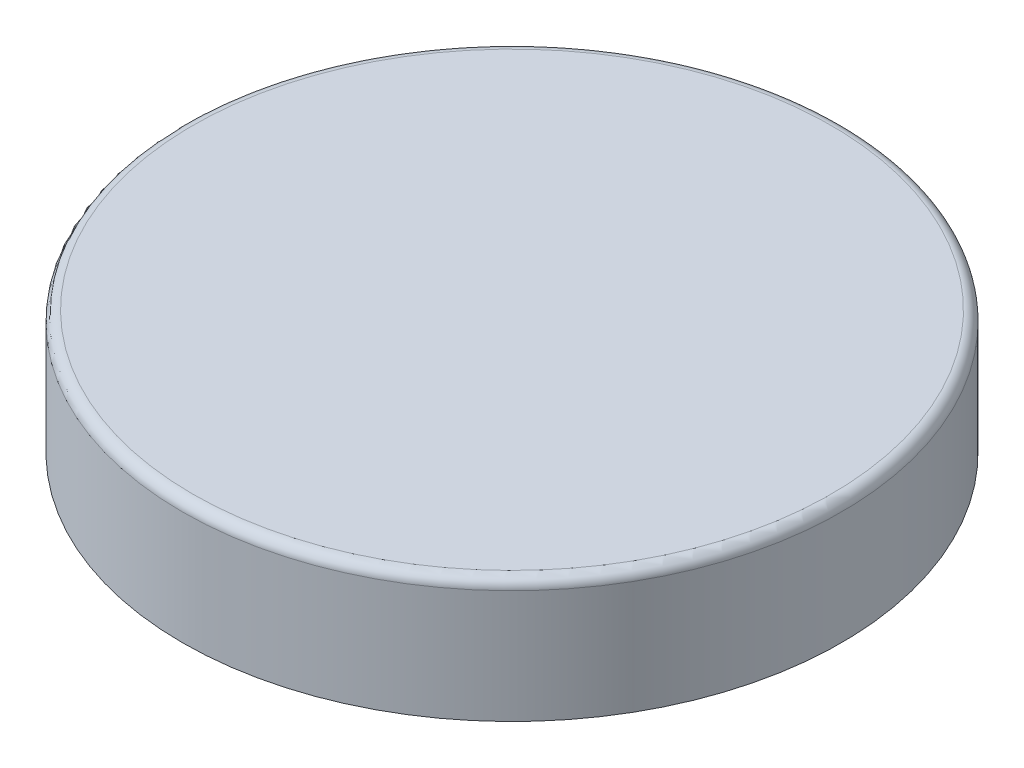
SolidWorks part; units mm, degrees
material "PLA Black"
ref_plane "Front Plane" through (0, 0, 0) normal (0, 0, 1) x (1, 0, 0)
ref_plane "Top Plane" through (0, 0, 0) normal (0, 1, 0) x (1, 0, 0)
ref_plane "Right Plane" through (0, 0, 0) normal (1, 0, 0) x (0, 0, -1)
sketch "Sketch1" plane through (0, 0, 0) normal (1, 0, 0) x (0, 0, -1)
  line L0 (0, -32.3252) -> (0, 32.3252) construction
  line L2 (0, 4.7625) -> (25.4, 4.7625)
  line L3 (25.4, 4.7625) -> (25.4, -4.7625)
  line L4 (25.4, -4.7625) -> (22.225, -4.7625)
  line L5 (22.225, -4.7625) -> (22.225, 1.5875)
  line L6 (22.225, 1.5875) -> (0, 1.5875)
  line L7 (0, 1.5875) -> (0, 4.7625)
  point P4 (0, 0)
  point P12 (25.4, 0)
  dimension "D1" = 3.175
  dimension "D2" = 3.175
  dimension "D3" = 6.35
  dimension "D4" = 50.8
revolve "Revolve1" add sketch "Sketch1" angle 360 about L0
fillet "Fillet1" radius 0.7937 3 edges at (0, 1.5875, -22.225) (0, -4.7625, -22.225) (0, 4.7625, -25.4)
